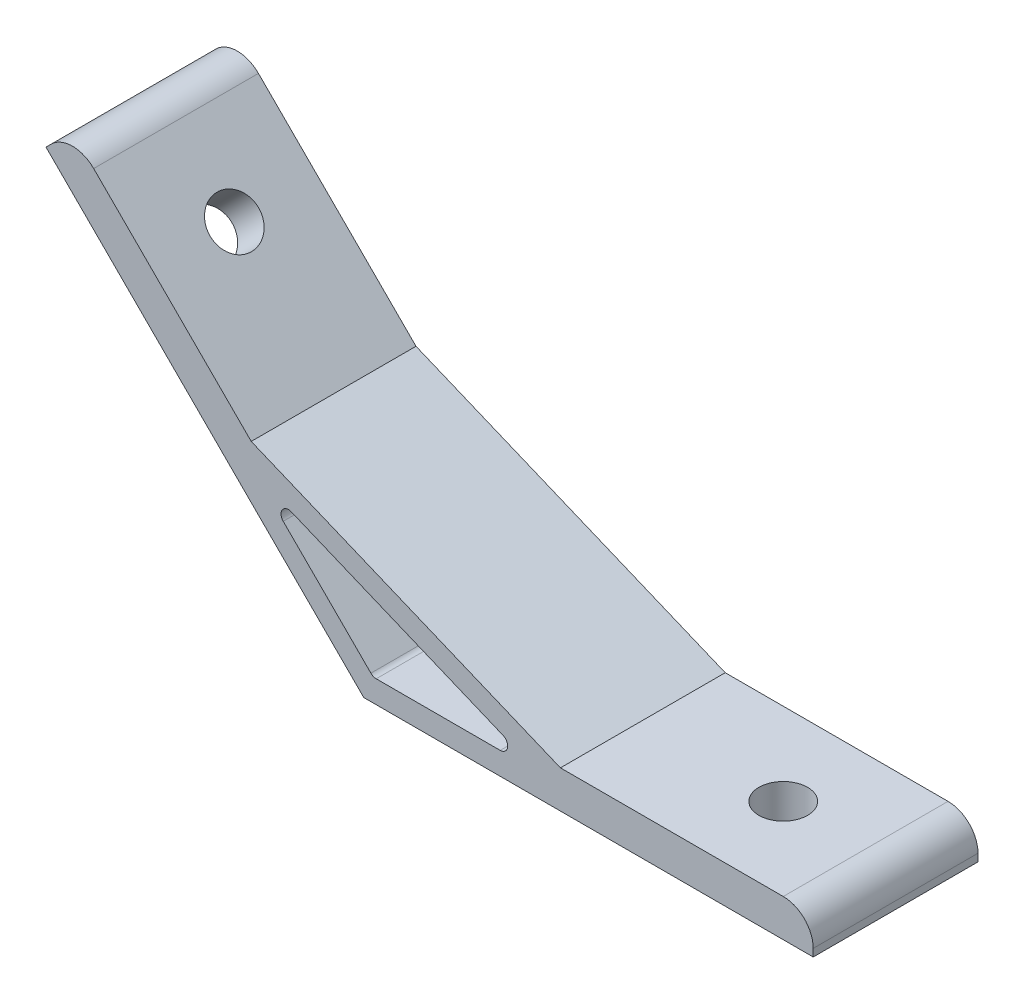
SolidWorks part; units mm, degrees
material "6063 T5"
ref_plane "Спереди" through (0, 0, 0) normal (0, 0, 1) x (1, 0, 0)
ref_plane "Сверху" through (0, 0, 0) normal (0, 1, 0) x (1, 0, 0)
ref_plane "Справа" through (0, 0, 0) normal (1, 0, 0) x (0, 0, -1)
sketch "Эскиз1" plane through (0, 0, 0) normal (0, 0, 1) x (1, 0, 0)
  line L0 (0, 0) -> (-42.4264, 42.4264)
  line L1 (-42.4264, 42.4264) -> (-38.8909, 45.9619)
  line L2 (-38.8909, 45.9619) -> (-15.0286, 22.0996)
  line L3 (-15.0286, 22.0996) -> (26.2536, 5)
  line L4 (26.2536, 5) -> (60, 5)
  line L5 (60, 5) -> (60, 0)
  line L6 (60, 0) -> (0, 0)
  line L7 (-14.3137, 18.5563) -> (23.2426, 3)
  line L8 (23.2426, 3) -> (1.2426, 3)
  line L9 (1.2426, 3) -> (-14.3137, 18.5563)
  line L10 (12.2426, 3) -> (12.2426, 0) construction
  line L11 (-6.5355, 10.7782) -> (-8.6569, 8.6569) construction
  line L12 (0, 0) -> (4.4645, 10.7782) construction
  dimension "D1" = 60
  dimension "D2" = 135
  dimension "D3" = 3
  dimension "D4" = 5
  dimension "D5" = 3
  dimension "D6" = 22
extrude "Бобышка-Вытянуть1" add sketch "Эскиз1" along normal mid plane 22
sketch "Эскиз2" plane through (0, 0, 0) normal (-0.7071, -0.7071, 0) x (0, 0, 1)
  line L0 (11, 60) -> (-11, 60) construction
  circle A0 centre (0, 45) radius 3.25
  dimension "D1" = 6.5
  dimension "D2" = 15
extrude "Вырез-Вытянуть1" cut sketch "Эскиз2" against normal up to surface (5 mm away) up to face at (-26.9597, 34.0308, 0)
sketch "Эскиз3" plane through (0, 0, 0) normal (0, -1, 0) x (1, 0, 0)
  line L0 (60, 11) -> (60, -11) construction
  circle A0 centre (45, 0) radius 3.25
  dimension "D1" = 6.5
  dimension "D2" = 15
extrude "Вырез-Вытянуть2" cut sketch "Эскиз3" against normal up to surface (5 mm away) up to face at (43.1268, 5, 0)
fillet "Скругление1" radius 4 2 edges at (60, 5, 0) (-38.8909, 45.9619, 0)
fillet "Скругление2" radius 1 3 edges at (-14.3137, 18.5563, 0) (1.2426, 3, 0) (23.2426, 3, 0)
